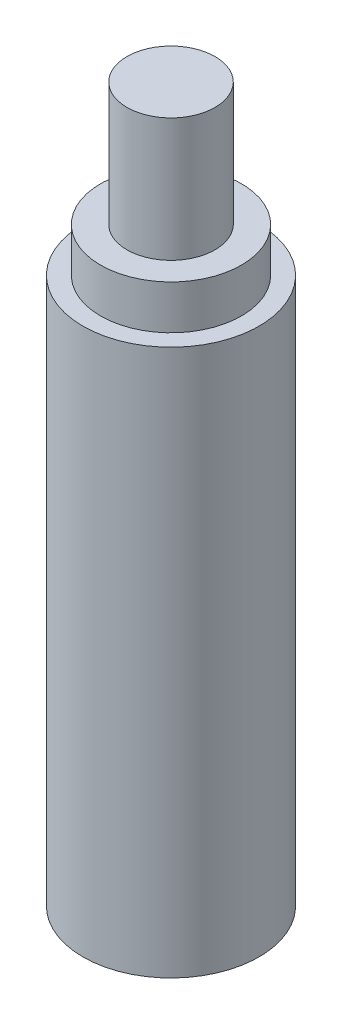
SolidWorks part; units mm, degrees
ref_plane "Plan de face" through (0, 0, 0) normal (0, 0, 1) x (1, 0, 0)
ref_plane "Plan de dessus" through (0, 0, 0) normal (0, 1, 0) x (1, 0, 0)
ref_plane "Plan de droite" through (0, 0, 0) normal (1, 0, 0) x (0, 0, -1)
sketch "Esquisse1" plane through (0, 0, 0) normal (0, 1, 0) x (1, 0, 0)
  circle A0 centre (0, 0) radius 10
extrude "Boss.-Extru.1" add sketch "Esquisse1" along normal blind 62
sketch "Esquisse2" plane through (0, 62, 0) normal (0, 1, 0) x (1, 0, 0)
  circle A0 centre (0, 0) radius 8
extrude "Boss.-Extru.2" add sketch "Esquisse2" along normal blind 5
sketch "Esquisse3" plane through (0, 67, 0) normal (0, 1, 0) x (1, 0, 0)
  circle A0 centre (0, 0) radius 5
extrude "Boss.-Extru.3" add sketch "Esquisse3" along normal blind 14
